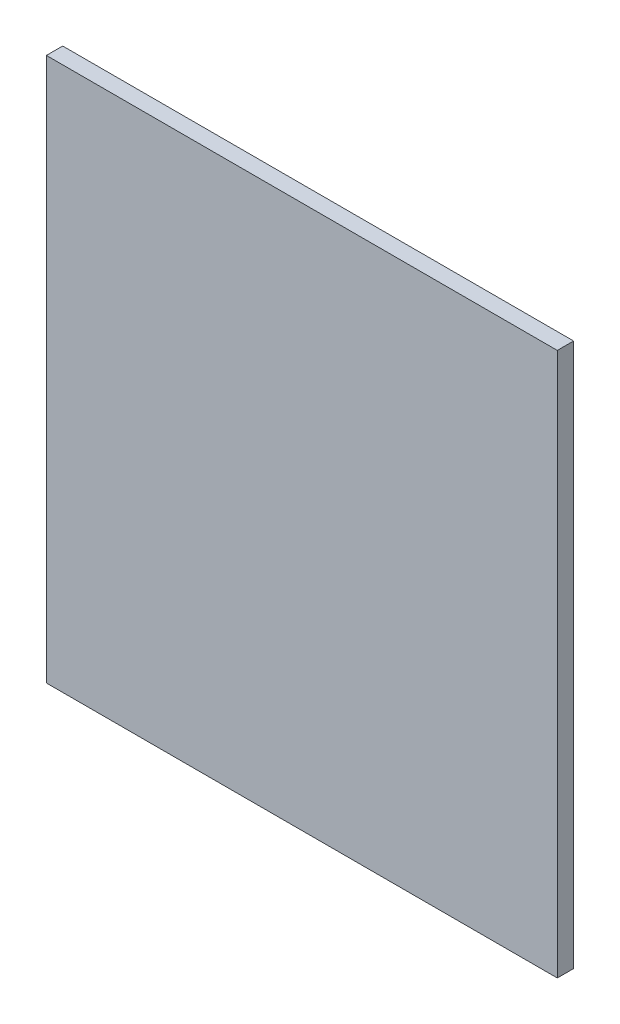
SolidWorks part; units mm, degrees
ref_plane "Front Plane" through (0, 0, 0) normal (0, 0, 1) x (1, 0, 0)
ref_plane "Top Plane" through (0, 0, 0) normal (0, 1, 0) x (1, 0, 0)
ref_plane "Right Plane" through (0, 0, 0) normal (1, 0, 0) x (0, 0, -1)
sketch "Sketch1" plane through (0, 0, 0) normal (0, 0, 1) x (1, 0, 0)
  line L1 (282, -300) -> (-282, -300)
  line L2 (282, -300) -> (282, 300)
  line L3 (282, 300) -> (-282, 300)
  line L4 (-282, -300) -> (-282, 300)
  line L5 (282, -300) -> (-282, 300) construction
  line L6 (282, 300) -> (-282, -300) construction
  point P0 (0, 0)
  dimension "D1" = 600
  dimension "D2" = 564
extrude "Boss-Extrude1" add sketch "Sketch1" along normal blind 18
equation "\"H_DSP\"=18"
equation "\"D1@Boss-Extrude1\"=\"H_DSP\""
equation "\"D2@Sketch1\"=600-2*\"H_DSP\""
